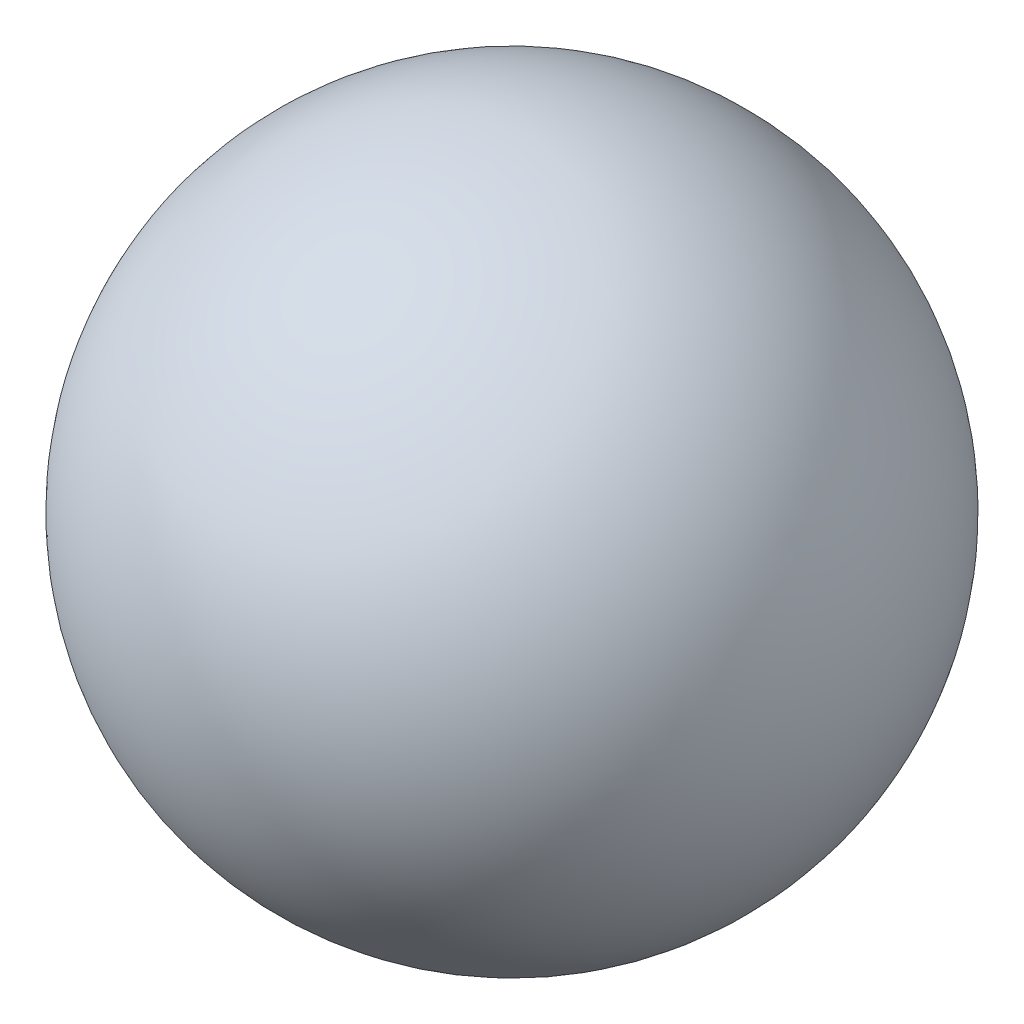
SolidWorks part; units mm, degrees
ref_plane "Front Plane" through (0, 0, 0) normal (0, 0, 1) x (1, 0, 0)
ref_plane "Top Plane" through (0, 0, 0) normal (0, 1, 0) x (1, 0, 0)
ref_plane "Right Plane" through (0, 0, 0) normal (1, 0, 0) x (0, 0, -1)
ref_plane "Plane1" through (0, 0, 0) normal (0, 0, 1) x (1, 0, 0)
sketch "Sketch1" plane through (0, 0, 0) normal (0, 0, 1) x (1, 0, 0)
  line L0 (0.45, 0) -> (-0.45, 0)
  line L1 (0.45, 0) -> (-0.45, 0) construction
  arc A0 (-0.45, 0) -> (0.45, 0) centre (0, 0) cw
revolve "Revolve1" add sketch "Sketch1" angle 360 about L1
